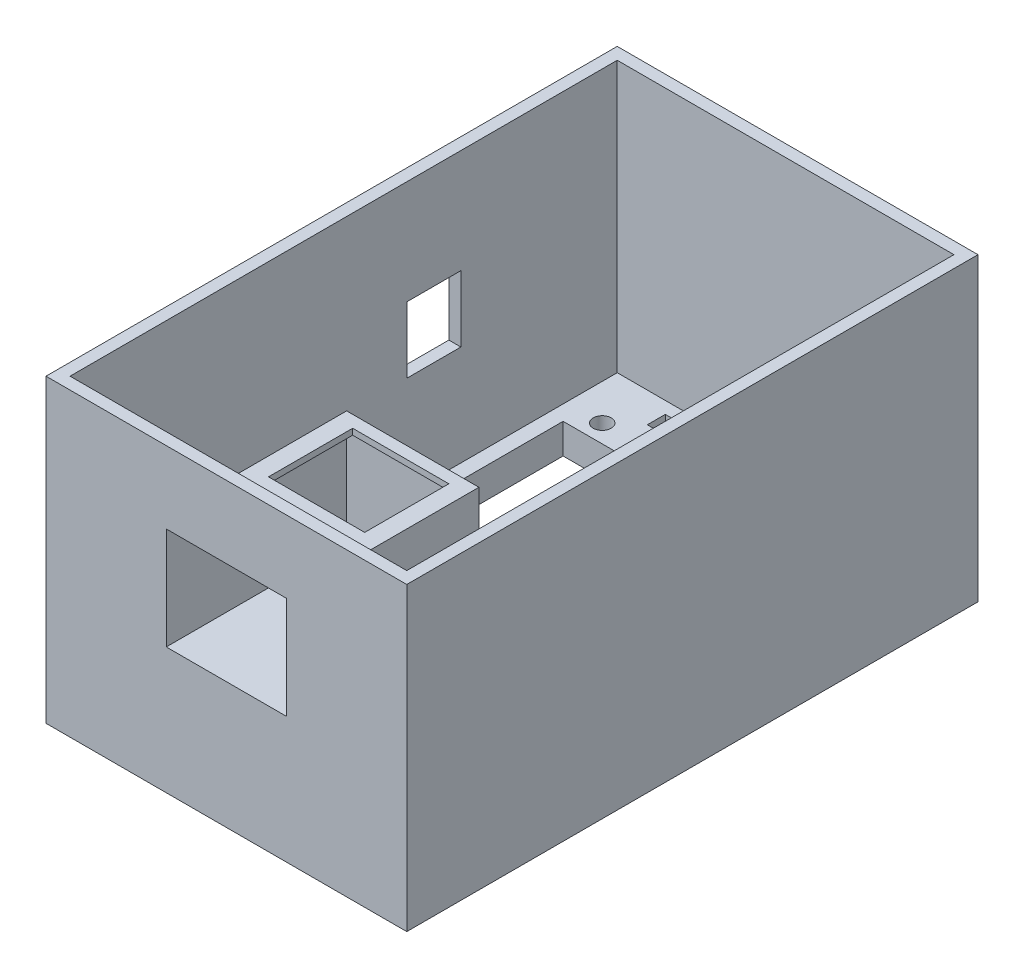
SolidWorks part; units mm, degrees
ref_plane "前基準面" through (0, 0, 0) normal (0, 0, 1) x (1, 0, 0)
ref_plane "上基準面" through (0, 0, 0) normal (0, 1, 0) x (1, 0, 0)
ref_plane "右基準面" through (0, 0, 0) normal (1, 0, 0) x (0, 0, -1)
sketch "草圖2" plane through (0, 0, 0) normal (0, 1, 0) x (1, 0, 0)
  line L1 (0, 0) -> (60, 0)
  line L2 (0, 0) -> (0, 95)
  line L3 (0, 95) -> (60, 95)
  line L4 (60, 0) -> (60, 95)
  dimension "D1" = 60
  dimension "D2" = 95
extrude "填料-伸長1" add sketch "草圖2" along normal blind 45
sketch "草圖3" plane through (0, 45, 0) normal (0, 1, 0) x (1, 0, 0)
  line L1 (2, 2) -> (58, 2)
  line L2 (2, 2) -> (2, 93)
  line L3 (2, 93) -> (58, 93)
  line L4 (58, 2) -> (58, 93)
  dimension "D1" = 91
  dimension "D2" = 56
sketch "草圖4" plane through (0, 45, 0) normal (0, 1, 0) x (1, 0, 0)
extrude "除料-伸長1" cut sketch "草圖3" against normal blind 40
sketch "草圖5" plane through (0, 5, 0) normal (0, 1, 0) x (1, 0, 0)
  line L1 (4.5, 11.5) -> (55.5, 11.5)
  line L2 (4.5, 11.5) -> (4.5, 81.5)
  line L3 (4.5, 81.5) -> (55.5, 81.5)
  line L4 (55.5, 11.5) -> (55.5, 81.5)
  dimension "D1" = 51
  dimension "D2" = 70
extrude "除料-伸長2" cut sketch "草圖5" against normal blind 5
sketch "草圖6" plane through (0, 5, 0) normal (0, 1, 0) x (1, 0, 0)
  circle A0 centre (8, 8.5) radius 1.5
  circle A1 centre (52, 8.5) radius 1.5
  circle A2 centre (8, 84.5) radius 1.5
  circle A3 centre (52, 84.5) radius 1.5
  dimension "D1" = 44
  dimension "D2" = 44
  dimension "D4" = 76
  dimension "D3" = 76
extrude "除料-伸長3" cut sketch "草圖6" against normal blind 5
sketch "草圖7" plane through (0, 0, 0) normal (0, -1, 0) x (-1, 0, 0)
sketch "草圖8" plane through (0, 0, 0) normal (0, -1, 0) x (-1, 0, 0)
  circle A0 centre (-8, 84.5) radius 2.75
  circle A1 centre (-8, 8.5) radius 2.75
  circle A2 centre (-52, 8.5) radius 2.75
  circle A3 centre (-52, 84.5) radius 2.75
extrude "除料-伸長4" cut sketch "草圖8" against normal blind 2.5
sketch "草圖9" plane through (0, 5, 0) normal (0, 1, 0) x (1, 0, 0)
sketch "草圖10" plane through (0, 5, 0) normal (0, 1, 0) x (1, 0, 0)
  line L0 (60, 95) -> (0, 95) construction
  line L1 (12, 88) -> (48, 88)
  line L2 (12, 88) -> (12, 91)
  line L3 (12, 91) -> (48, 91)
  line L4 (48, 88) -> (48, 91)
  dimension "D1" = 36
  dimension "D2" = 3
  dimension "D3" = 7
extrude "除料-伸長5" cut sketch "草圖10" against normal blind 2
ref_plane "平面1" through (0, 45, 0) normal (0, -1, 0) x (-1, 0, 0)
sketch "草圖11" plane through (0, 45, 0) normal (0, -1, 0) x (1, 0, 0)
  line L1 (60, 0) -> (0, 0)
  line L2 (60, 0) -> (60, -95)
  line L3 (60, -95) -> (0, -95)
  line L4 (0, 0) -> (0, -95)
extrude "填料-伸長2" add sketch "草圖11" against normal blind 5
sketch "草圖12" plane through (0, 50, 0) normal (0, 1, 0) x (1, 0, 0)
  line L1 (2, 2) -> (58, 2)
  line L2 (2, 2) -> (2, 93)
  line L3 (2, 93) -> (58, 93)
  line L4 (58, 2) -> (58, 93)
  dimension "D1" = 56
  dimension "D2" = 91
extrude "除料-伸長6" cut sketch "草圖12" against normal blind 5
sketch "草圖13" plane through (0, 0, 0) normal (-1, 0, 0) x (0, 0, 1)
  line L1 (-58, 32.7) -> (-67, 32.7)
  line L2 (-58, 32.7) -> (-58, 21.7)
  line L3 (-58, 21.7) -> (-67, 21.7)
  line L4 (-67, 32.7) -> (-67, 21.7)
  dimension "D1" = 11
  dimension "D2" = 9
extrude "除料-伸長7" cut sketch "草圖13" against normal blind 5
sketch "草圖14" plane through (0, 0, 0) normal (0, 0, 1) x (1, 0, 0)
  line L1 (41, 39) -> (19, 39)
  line L2 (41, 39) -> (41, 20)
  line L3 (41, 20) -> (19, 20)
  line L4 (19, 39) -> (19, 20)
  dimension "D1" = 22
  dimension "D2" = 19
extrude "填料-伸長3" add sketch "草圖14" against normal blind 31
sketch "草圖15" plane through (0, 0, 0) normal (0, 0, 1) x (1, 0, 0)
  line L1 (40, 38) -> (20, 38)
  line L2 (40, 38) -> (40, 21)
  line L3 (40, 21) -> (20, 21)
  line L4 (20, 38) -> (20, 21)
  dimension "D1" = 17
  dimension "D2" = 20
extrude "除料-伸長8" cut sketch "草圖15" against normal blind 30
sketch "草圖16" plane through (0, 39, 0) normal (0, 1, 0) x (1, 0, 0)
  line L1 (22, 15) -> (38, 15)
  line L2 (22, 15) -> (22, 29)
  line L3 (22, 29) -> (38, 29)
  line L4 (38, 15) -> (38, 29)
  dimension "D1" = 16
  dimension "D2" = 14
extrude "除料-伸長9" cut sketch "草圖16" against normal blind 2
